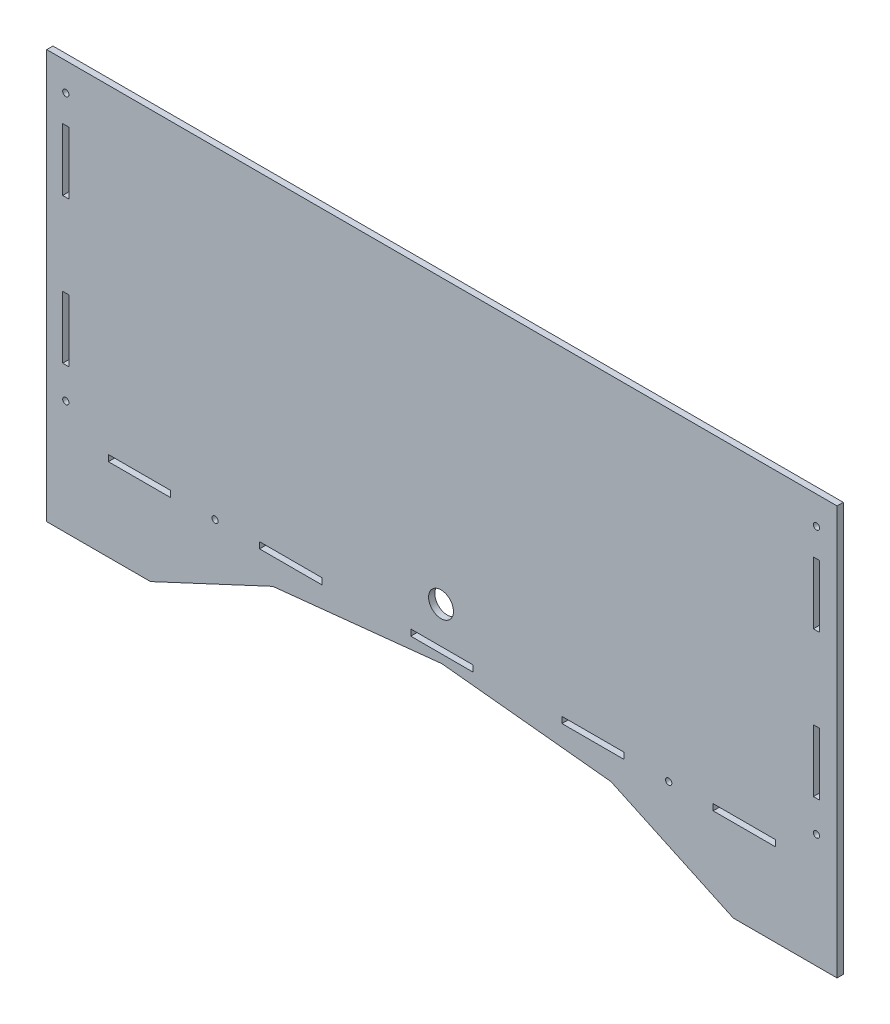
SolidWorks part; units mm, degrees
ref_plane "Front Plane" through (0, 0, 0) normal (0, 0, 1) x (1, 0, 0)
ref_plane "Top Plane" through (0, 0, 0) normal (0, 1, 0) x (1, 0, 0)
ref_plane "Right Plane" through (0, 0, 0) normal (1, 0, 0) x (0, 0, -1)
sketch "Sketch1" plane through (-12.6118, -16.6961, 0) normal (0, 0, 1) x (0, -1, 0)
  line L10 (-213.6961, 12.6118) -> (-213.6961, 393.4518)
  line L11 (-213.6961, 393.4518) -> (-16.6961, 393.4518)
  line L12 (-16.6961, 393.4518) -> (-16.6961, 343.4518)
  line L13 (-16.6961, 343.4518) -> (-44.1663, 284.5418)
  line L14 (-44.1663, 284.5418) -> (-52.6369, 203.0318)
  line L15 (-52.6369, 203.0318) -> (-44.1663, 121.5218)
  line L16 (-44.1663, 121.5218) -> (-16.6961, 62.6118)
  line L17 (-16.6961, 62.6118) -> (-16.6961, 12.6118)
  line L18 (-16.6961, 12.6118) -> (-213.6961, 12.6118)
  line L19 (-59.5933, 290.8875) -> (-56.5933, 333.7475) construction
  line L20 (-186.6799, 20.3118) -> (-156.6799, 20.3118)
  line L21 (-186.6799, 20.3118) -> (-186.6799, 23.3118)
  line L22 (-186.6799, 23.3118) -> (-156.6799, 23.3118)
  line L23 (-156.6799, 20.3118) -> (-156.6799, 23.3118)
  line L24 (-116.6799, 20.3118) -> (-86.6799, 20.3118)
  line L25 (-116.6799, 20.3118) -> (-116.6799, 23.3118)
  line L26 (-116.6799, 23.3118) -> (-86.6799, 23.3118)
  line L27 (-86.6799, 20.3118) -> (-86.6799, 23.3118)
  line L28 (-59.5933, 42.3161) -> (-56.5933, 42.3161)
  line L29 (-59.5933, 42.3161) -> (-59.5933, 72.3161)
  line L30 (-59.5933, 72.3161) -> (-56.5933, 72.3161)
  line L31 (-56.5933, 42.3161) -> (-56.5933, 72.3161)
  line L32 (-59.6369, 115.1732) -> (-56.6369, 115.1732)
  line L33 (-59.6369, 115.1732) -> (-59.6369, 145.1732)
  line L34 (-59.6369, 145.1732) -> (-56.6369, 145.1732)
  line L35 (-56.6369, 115.1732) -> (-56.6369, 145.1732)
  line L36 (-59.6369, 188.0303) -> (-56.6369, 188.0303)
  line L37 (-59.6369, 188.0303) -> (-59.6369, 218.0303)
  line L38 (-59.6369, 218.0303) -> (-56.6369, 218.0303)
  line L39 (-56.6369, 188.0303) -> (-56.6369, 218.0303)
  line L40 (-59.5933, 260.8875) -> (-56.5933, 260.8875)
  line L41 (-59.5933, 260.8875) -> (-59.5933, 290.8875)
  line L42 (-59.5933, 290.8875) -> (-56.5933, 290.8875)
  line L43 (-56.5933, 260.8875) -> (-56.5933, 290.8875)
  line L44 (-59.5933, 333.7475) -> (-56.5933, 333.7475)
  line L45 (-59.5933, 333.7475) -> (-59.5933, 363.7475)
  line L46 (-59.5933, 363.7475) -> (-56.5933, 363.7475)
  line L47 (-56.5933, 333.7475) -> (-56.5933, 363.7475)
  line L48 (-59.5933, 42.3161) -> (-59.5933, 12.6118) construction
  line L49 (-86.6961, 382.0318) -> (-116.6961, 382.0318)
  line L50 (-86.6961, 382.0318) -> (-86.6961, 385.0318)
  line L51 (-86.6961, 385.0318) -> (-116.6961, 385.0318)
  line L52 (-116.6961, 382.0318) -> (-116.6961, 385.0318)
  line L53 (-186.6961, 382.0318) -> (-156.6961, 382.0318)
  line L54 (-186.6961, 382.0318) -> (-186.6961, 385.0318)
  line L55 (-186.6961, 385.0318) -> (-156.6961, 385.0318)
  line L56 (-156.6961, 382.0318) -> (-156.6961, 385.0318)
  line L57 (-59.5933, 363.7475) -> (-59.5933, 393.4518) construction
  line L58 (-156.6961, 385.0318) -> (-116.6961, 385.0318) construction
  line L60 (-200.1961, 383.5318) -> (-186.6961, 383.5318) construction
  line L62 (-71.6961, 383.5318) -> (-86.6961, 383.5318) construction
  line L63 (-156.6799, 23.3118) -> (-116.6799, 23.3118) construction
  line L65 (-186.6799, 21.8118) -> (-200.1799, 21.8118) construction
  line L67 (-86.6799, 21.8118) -> (-71.6799, 21.8118) construction
  circle A4 centre (-200.1799, 21.8118) radius 1.5
  circle A5 centre (-58.0933, 312.3175) radius 1.5
  circle A6 centre (-200.1961, 383.5318) radius 1.5
  circle A7 centre (-71.6961, 383.5318) radius 1.5
  circle A8 centre (-58.1369, 93.7446) radius 1.5
  circle A9 centre (-71.6799, 21.8118) radius 1.5
  circle A10 centre (-77.2413, 202.6118) radius 6
  point P7 (0, 0)
  point P9 (-186.6961, 383.5318)
  point P10 (0, 0)
  point P12 (-86.6961, 383.5318)
  dimension "D1" = 12
  dimension "D44" = 3
  dimension "D53" = 3
  dimension "D54" = 3
  dimension "D55" = 3
  dimension "D2" = 364.72
  dimension "D9" = 30
  dimension "D10" = 42.86
  dimension "D36" = 15
  dimension "D38" = 8.42
  dimension "D39" = 70
  dimension "D41" = 13.5
  dimension "D43" = 13.5
  dimension "D45" = 3
  dimension "D46" = 30
  dimension "D47" = 155
  dimension "D48" = 199.067
  dimension "D49" = 168.134
  dimension "D50" = 160.933
  dimension "D51" = 4
  dimension "D52" = 65
  dimension "D56" = 197
  dimension "D57" = 50
  dimension "D58" = 13.5163
  dimension "D60" = 30
  dimension "D61" = 3
  dimension "D62" = 13.5
  dimension "D63" = 40
  dimension "D64" = 3
  dimension "D65" = 30
  dimension "D66" = 7.7
  dimension "D68" = 15
  dimension "D70" = 3
  dimension "D71" = 30
  dimension "D72" = 39.8972
  dimension "D73" = 3
  dimension "D75" = 42.8571
  dimension "D76" = 3
  dimension "D77" = 30
  dimension "D80" = 21.4286
  dimension "D81" = 21.4286
  dimension "D82" = 30
  dimension "D83" = 3
  dimension "D84" = 3
  dimension "D85" = 30
  dimension "D86" = 42.8571
extrude "Boss-Extrude1" add sketch "Sketch1" along normal blind 3
